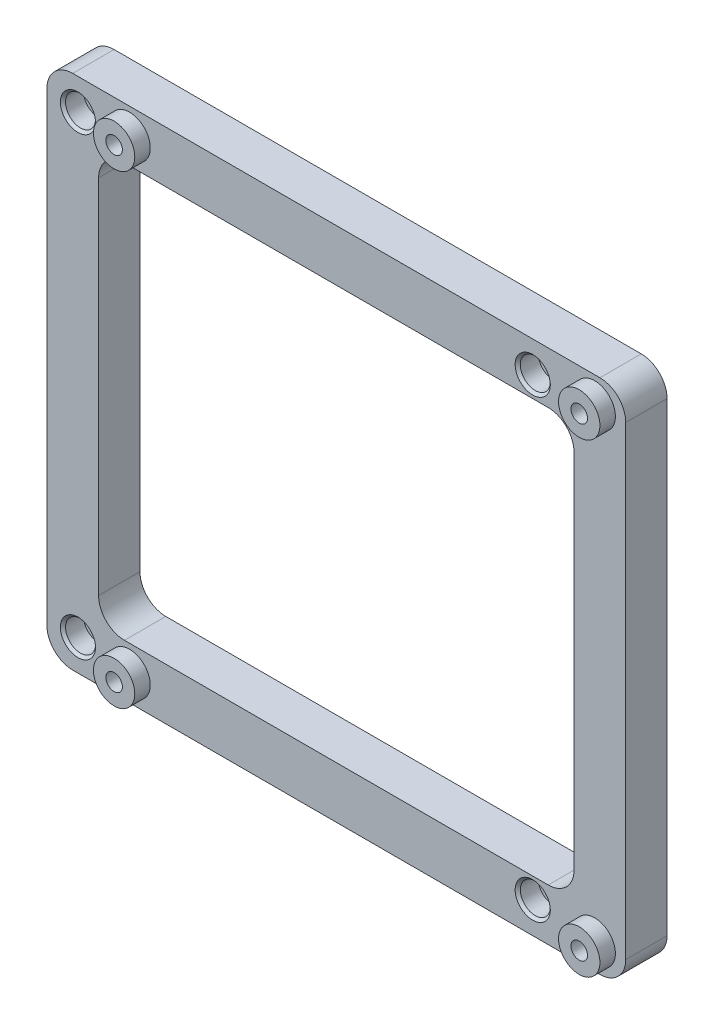
SolidWorks part; units mm, degrees
ref_plane "Přední rovina" through (0, 0, 0) normal (0, 0, 1) x (1, 0, 0)
ref_plane "Horní rovina" through (0, 0, 0) normal (0, 1, 0) x (1, 0, 0)
ref_plane "Pravá rovina" through (0, 0, 0) normal (1, 0, 0) x (0, 0, -1)
sketch "Skica1" plane through (0, 0, 0) normal (0, 0, 1) x (1, 0, 0)
  line L0 (-49, 49) -> (49, 49) construction
  line L1 (-50, -50) -> (50, -50) construction
  line L2 (-50, -50) -> (-50, 50) construction
  line L3 (-50, 50) -> (50, 50) construction
  line L4 (50, -50) -> (50, 50) construction
  line L5 (-50, -50) -> (50, 50) construction
  line L6 (-50, 50) -> (50, -50) construction
  line L7 (-44, 44) -> (44, 44) construction
  line L8 (-44, 44) -> (-44, -44) construction
  line L9 (44, 44) -> (44, -44) construction
  line L10 (-50, 45) -> (56, 45) construction
  line L11 (-50, 0) -> (50, 0) construction
  line L12 (-34, 41.7668) -> (-31.2, 43.3834)
  line L13 (-31.2, 43.3834) -> (-31.2, 46.6166)
  line L14 (-31.2, 46.6166) -> (-34, 48.2332)
  line L15 (-34, 48.2332) -> (-36.8, 46.6166)
  line L16 (-36.8, 46.6166) -> (-36.8, 43.3834)
  line L17 (-36.8, 43.3834) -> (-34, 41.7668)
  line L18 (56, 41.7668) -> (58.8, 43.3834)
  line L19 (58.8, 43.3834) -> (58.8, 46.6166)
  line L20 (58.8, 46.6166) -> (56, 48.2332)
  line L21 (56, 48.2332) -> (53.2, 46.6166)
  line L22 (53.2, 46.6166) -> (53.2, 43.3834)
  line L23 (53.2, 43.3834) -> (56, 41.7668)
  line L24 (53.2, -43.3834) -> (56, -41.7668)
  line L25 (53.2, -46.6166) -> (53.2, -43.3834)
  line L26 (56, -48.2332) -> (53.2, -46.6166)
  line L27 (58.8, -46.6166) -> (56, -48.2332)
  line L28 (58.8, -43.3834) -> (58.8, -46.6166)
  line L29 (56, -41.7668) -> (58.8, -43.3834)
  line L30 (-36.8, -43.3834) -> (-34, -41.7668)
  line L31 (-36.8, -46.6166) -> (-36.8, -43.3834)
  line L32 (-34, -48.2332) -> (-36.8, -46.6166)
  line L33 (-31.2, -46.6166) -> (-34, -48.2332)
  line L34 (-31.2, -43.3834) -> (-31.2, -46.6166)
  line L35 (-34, -41.7668) -> (-31.2, -43.3834)
  line L36 (-50, 50) -> (62, 50)
  line L37 (62, 50) -> (62, -50)
  line L38 (62, -50) -> (-50, -50)
  line L39 (-50, -50) -> (-50, 50)
  line L40 (-40, -40) -> (52, -40)
  line L41 (-40, -40) -> (-40, 40)
  line L42 (-40, 40) -> (52, 40)
  line L43 (52, 40) -> (52, -40)
  line L44 (56, 45) -> (56, -45.0379) construction
  circle A0 centre (-44, 44) radius 1.6
  circle A1 centre (44, 44) radius 1.6
  circle A2 centre (-44, -44) radius 1.6
  circle A3 centre (44, -44) radius 1.6
  circle A4 centre (-34, 45) radius 2.8 construction
  circle A5 centre (56, 45) radius 2.8 construction
  circle A6 centre (-44, 44) radius 2.85 construction
  point P0 (0, 0)
  dimension "D4" = 3.2
  dimension "D7" = 5.7
  dimension "D1" = 100
  dimension "D2" = 1
  dimension "D3" = 5
  dimension "D5" = 5
  dimension "D6" = 5.6
  dimension "D8" = 10
  dimension "D9" = 90
  dimension "D10" = 10
  dimension "D11" = 10
  dimension "D12" = 6
  dimension "D13" = 6
extrude "Přidat vysunutím1" add sketch "Skica1" along normal blind 8
sketch "Skica2" plane through (0, 0, 8) normal (0, 0, 1) x (1, 0, 0)
  circle A0 centre (-44, 44) radius 2.9
  circle A1 centre (44, 44) radius 2.9
  circle A2 centre (44, -44) radius 2.9
  circle A3 centre (-44, -44) radius 2.9
  dimension "D1" = 5.8
extrude "Odebrat vysunutím1" cut sketch "Skica2" against normal blind 4
sketch "Skica3" plane through (0, 0, 8) normal (0, 0, 1) x (1, 0, 0)
  line L0 (-31.2, -46.6166) -> (-31.2, -43.3834) construction
  line L1 (-34, -48.2332) -> (-31.2, -46.6166) construction
  line L2 (-36.8, -46.6166) -> (-34, -48.2332) construction
  line L3 (-36.8, -43.3834) -> (-36.8, -46.6166) construction
  line L4 (-34, -41.7668) -> (-36.8, -43.3834) construction
  line L5 (-31.2, -43.3834) -> (-34, -41.7668) construction
  line L6 (58.8, -46.6166) -> (58.8, -43.3834) construction
  line L7 (56, -48.2332) -> (58.8, -46.6166) construction
  line L8 (53.2, -46.6166) -> (56, -48.2332) construction
  line L9 (53.2, -43.3834) -> (53.2, -46.6166) construction
  line L10 (56, -41.7668) -> (53.2, -43.3834) construction
  line L11 (58.8, -43.3834) -> (56, -41.7668) construction
  line L12 (53.2, 46.6166) -> (53.2, 43.3834) construction
  line L13 (56, 48.2332) -> (53.2, 46.6166) construction
  line L14 (58.8, 46.6166) -> (56, 48.2332) construction
  line L15 (58.8, 43.3834) -> (58.8, 46.6166) construction
  line L16 (56, 41.7668) -> (58.8, 43.3834) construction
  line L17 (53.2, 43.3834) -> (56, 41.7668) construction
  line L18 (-34, 48.2332) -> (-36.8, 46.6166) construction
  line L19 (-36.8, 46.6166) -> (-36.8, 43.3834) construction
  line L20 (-36.8, 43.3834) -> (-34, 41.7668) construction
  line L21 (-34, 41.7668) -> (-31.2, 43.3834) construction
  line L22 (-31.2, 43.3834) -> (-31.2, 46.6166) construction
  line L23 (-31.2, 46.6166) -> (-34, 48.2332) construction
  line L24 (-31.2, -46.6166) -> (-31.2, -43.3834)
  line L25 (-34, -48.2332) -> (-31.2, -46.6166)
  line L26 (-36.8, -46.6166) -> (-34, -48.2332)
  line L27 (-36.8, -43.3834) -> (-36.8, -46.6166)
  line L28 (-34, -41.7668) -> (-36.8, -43.3834)
  line L29 (-31.2, -43.3834) -> (-34, -41.7668)
  line L30 (58.8, -46.6166) -> (58.8, -43.3834)
  line L31 (56, -48.2332) -> (58.8, -46.6166)
  line L32 (53.2, -46.6166) -> (56, -48.2332)
  line L33 (53.2, -43.3834) -> (53.2, -46.6166)
  line L34 (56, -41.7668) -> (53.2, -43.3834)
  line L35 (58.8, -43.3834) -> (56, -41.7668)
  line L36 (53.2, 46.6166) -> (53.2, 43.3834)
  line L37 (56, 48.2332) -> (53.2, 46.6166)
  line L38 (58.8, 46.6166) -> (56, 48.2332)
  line L39 (58.8, 43.3834) -> (58.8, 46.6166)
  line L40 (56, 41.7668) -> (58.8, 43.3834)
  line L41 (53.2, 43.3834) -> (56, 41.7668)
  line L42 (-34, 48.2332) -> (-36.8, 46.6166)
  line L43 (-36.8, 46.6166) -> (-36.8, 43.3834)
  line L44 (-36.8, 43.3834) -> (-34, 41.7668)
  line L45 (-34, 41.7668) -> (-31.2, 43.3834)
  line L46 (-31.2, 43.3834) -> (-31.2, 46.6166)
  line L47 (-31.2, 46.6166) -> (-34, 48.2332)
  line L48 (-34, 48.2332) -> (-34, 41.7668) construction
  line L49 (-36.8, 43.3834) -> (-31.2, 46.6166) construction
  line L50 (56, 48.2332) -> (56, 41.7668) construction
  line L51 (56, -48.2332) -> (56, -41.7668) construction
  line L52 (-34, -48.2332) -> (-34, -41.7668) construction
  circle A0 centre (-34, -45) radius 1.6
  circle A1 centre (56, -45) radius 1.6
  circle A2 centre (56, 45) radius 1.6
  circle A3 centre (-34, 45) radius 1.6
  dimension "D1" = 3.2
extrude "Přidat vysunutím2" add sketch "Skica3" against normal blind 4
chamfer "Zkosení1" distance 0.5 angle 45 4 edges at (46.9, -44, 8) (-41.1, -44, 8) (46.9, 44, 8) (-41.1, 44, 8)
fillet "Zaoblit1" radius 5 8 edges at (-40, -40, 4) (52, -40, 4) (52, 40, 4) (-40, 40, 4) (62, 50, 4) (-50, 50, 4) (62, -50, 4) (-50, -50, 4)
sketch "Skica4" plane through (0, 0, 8) normal (0, 0, 1) x (1, 0, 0)
  circle A0 centre (-34, 45) radius 4
  circle A1 centre (56, 45) radius 4
  circle A2 centre (56, -45) radius 4
  circle A3 centre (-34, -45) radius 4
  circle A4 centre (-34, -45) radius 1.6 construction
  circle A5 centre (56, -45) radius 1.6 construction
  circle A6 centre (56, 45) radius 1.6 construction
  circle A7 centre (-34, 45) radius 1.6 construction
  circle A8 centre (-34, -45) radius 1.6
  circle A9 centre (56, -45) radius 1.6
  circle A10 centre (56, 45) radius 1.6
  circle A11 centre (-34, 45) radius 1.6
  dimension "D1" = 8
extrude "Přidat vysunutím3" add sketch "Skica4" along normal blind 3
